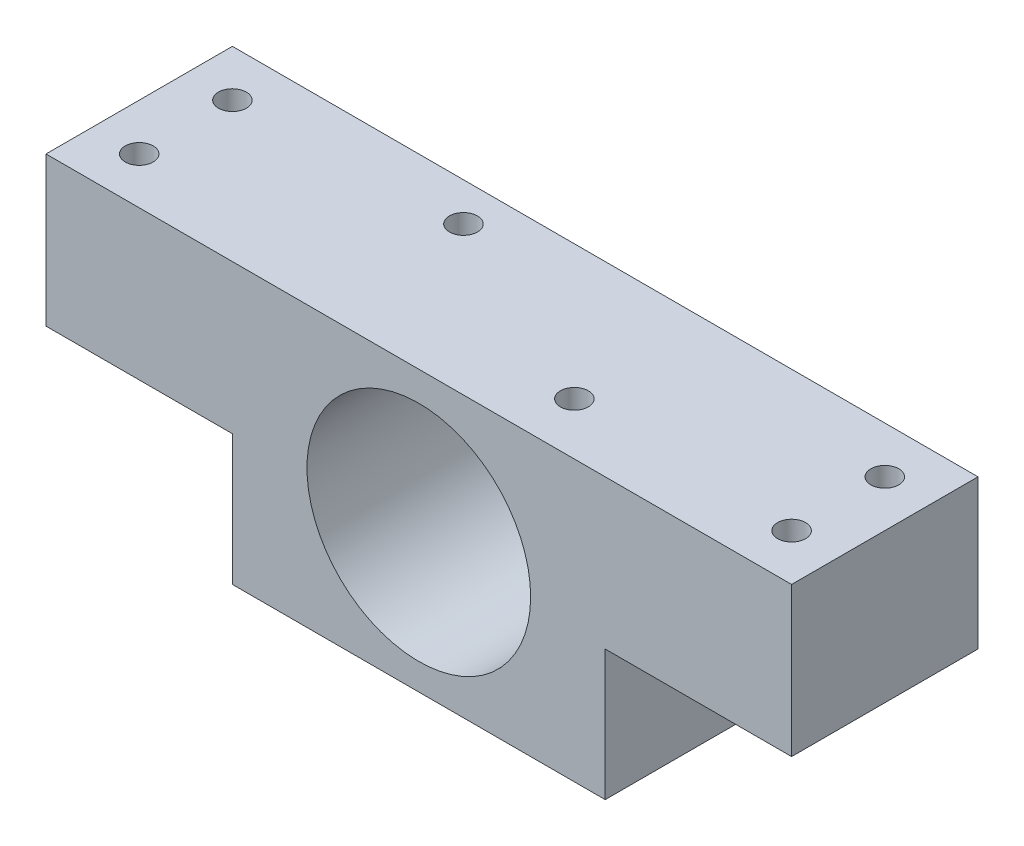
SolidWorks part; units mm, degrees
ref_plane "Front Plane" through (0, 0, 0) normal (0, 0, 1) x (1, 0, 0)
ref_plane "Top Plane" through (0, 0, 0) normal (0, 1, 0) x (1, 0, 0)
ref_plane "Right Plane" through (0, 0, 0) normal (1, 0, 0) x (0, 0, -1)
sketch "Sketch2" plane through (0, 0, 0) normal (0, 1, 0) x (1, 0, 0)
  line L1 (-40, -10) -> (40, -10)
  line L2 (-40, -10) -> (-40, 10)
  line L3 (-40, 10) -> (40, 10)
  line L4 (40, -10) -> (40, 10)
  line L5 (-40, -10) -> (40, 10) construction
  line L6 (-40, 10) -> (40, -10) construction
  point P0 (0, 0)
  dimension "D1" = 20
  dimension "D2" = 80
extrude "Boss-Extrude1" add sketch "Sketch2" along normal blind 30
sketch "Sketch3" plane through (0, 0, 10) normal (0, 0, 1) x (1, 0, 0)
  line L0 (0, 30) -> (0, 0) construction
  line L1 (-40, 30) -> (40, 30) construction
  line L2 (40, 14) -> (20, 14)
  line L3 (-40, 0) -> (-20, 0)
  line L4 (-40, 0) -> (-40, 14)
  line L5 (-40, 14) -> (-20, 14)
  line L6 (-20, 0) -> (-20, 14)
  line L7 (20, 0) -> (20, 14)
  line L8 (40, 0) -> (20, 0)
  line L9 (40, 0) -> (40, 14)
  dimension "D1" = 14
  dimension "D2" = 20
extrude "Cut-Extrude1" cut sketch "Sketch3" against normal blind 30
sketch "Sketch4" plane through (0, 0, 10) normal (0, 0, 1) x (1, 0, 0)
  line L0 (0, 0) -> (0, 30) construction
  line L1 (-40, 30) -> (40, 30) construction
  line L2 (-20, 14) -> (21.1655, 14) construction
  line L3 (40, 14) -> (20, 14) construction
  line L4 (0, 2.84) -> (-20, 2.84) construction
  line L5 (-20, 14) -> (-40, 14) construction
  circle A0 centre (0, 14.84) radius 12
  dimension "D1" = 24
  dimension "D2" = 11.16
extrude "Cut-Extrude2" cut sketch "Sketch4" against normal blind 30
sketch "Sketch5" plane through (0, 30, 0) normal (0, 1, 0) x (1, 0, 0)
  line L0 (-35, 10) -> (-35, -10) construction
  line L1 (40, 10) -> (-40, 10) construction
  line L2 (-40, -10) -> (40, -10) construction
  line L3 (0, 0) -> (0, 10) construction
  line L4 (0, 0) -> (-40, 0) construction
  line L5 (-40, 10) -> (-40, -10) construction
  circle A0 centre (-35, 5) radius 1.5
  circle A1 centre (-35, -5) radius 1.5
  circle A2 centre (35, -5) radius 1.5
  circle A3 centre (35, 5) radius 1.5
  dimension "D1" = 10
  dimension "D2" = 3
  dimension "D3" = 5
  dimension "D4" = 5
extrude "Cut-Extrude3" cut sketch "Sketch5" against normal blind 30
sketch "Sketch6" plane through (0, 30, 0) normal (0, 1, 0) x (1, 0, 0)
  line L6 (-40, 10) -> (-40, -10) construction
  circle A0 centre (-11.1, 5.89) radius 1.5
  circle A1 centre (11.1, -4.41) radius 1.5
  dimension "D3" = 3
  dimension "D4" = 3
  dimension "D6" = 51.1
  dimension "D5" = 28.9
extrude "Cut-Extrude4" cut sketch "Sketch6" against normal blind 3
